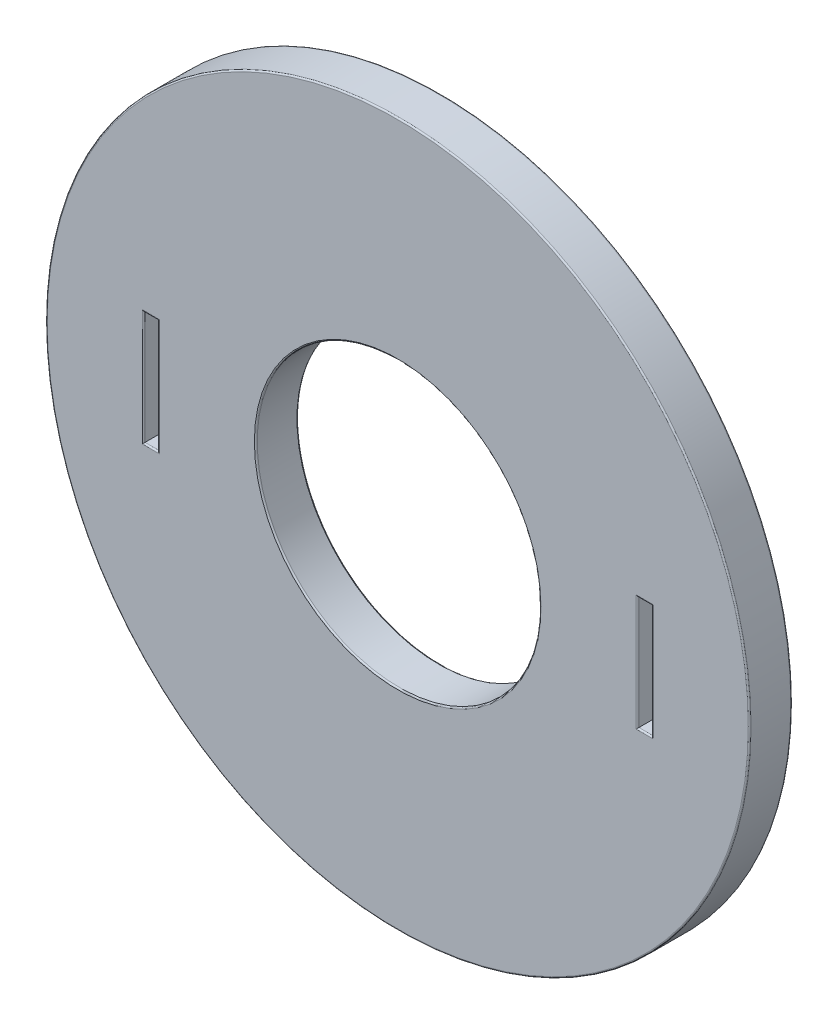
SolidWorks part; units mm, degrees
ref_plane "Ön Düzlem" through (0, 0, 0) normal (0, 0, 1) x (1, 0, 0)
ref_plane "Üst Düzlem" through (0, 0, 0) normal (0, 1, 0) x (1, 0, 0)
ref_plane "Sağ Düzlem" through (0, 0, 0) normal (1, 0, 0) x (0, 0, -1)
sketch "Sketch1" plane through (0, 0, 0) normal (0, 0, 1) x (1, 0, 0)
  circle A0 centre (0, 0) radius 12.4
  dimension "D1" = 24.8
extrude "Boss-Extrude1" add sketch "Sketch1" along normal blind 1.5
sketch "Sketch2" plane through (0, 0, 1.5) normal (0, 0, 1) x (1, 0, 0)
  line L0 (-12.4, 0) -> (12.4, 0) construction
  line L1 (-8.95, 2) -> (-8.45, 2)
  line L2 (-8.95, 2) -> (-8.95, -2)
  line L3 (-8.95, -2) -> (-8.45, -2)
  line L4 (-8.45, 2) -> (-8.45, -2)
  line L6 (8.45, 2) -> (8.95, 2)
  line L7 (8.45, 2) -> (8.45, -2)
  line L8 (8.45, -2) -> (8.95, -2)
  line L9 (8.95, 2) -> (8.95, -2)
  circle A0 centre (0, 0) radius 5
  circle A1 centre (0, 0) radius 12.4 construction
  dimension "D1" = 10
  dimension "D2" = 4
  dimension "D3" = 0.5
  dimension "D4" = 0.5
  dimension "D5" = 4
  dimension "D6" = 16.9
  dimension "D7" = 8.45
  dimension "D8" = 2
  dimension "D9" = 2
extrude "Cut-Extrude1" cut sketch "Sketch2" against normal through all
fillet "Fillet1" radius 0.05 20 edges at (12.4, 0, 1.5) (5, 0, 1.5) (-8.7, -2, 1.5) (-8.45, 0, 1.5) (-8.7, 2, 1.5) (-8.95, 0, 1.5) (8.7, -2, 1.5) (8.95, 0, 1.5) (8.7, 2, 1.5) (8.45, 0, 1.5) (12.4, 0, 0) (-8.7, -2, 0) (-8.95, 0, 0) (-8.45, 0, 0) (-8.7, 2, 0) (8.7, -2, 0) (8.95, 0, 0) (8.7, 2, 0) (8.45, 0, 0) (5, 0, 0)
